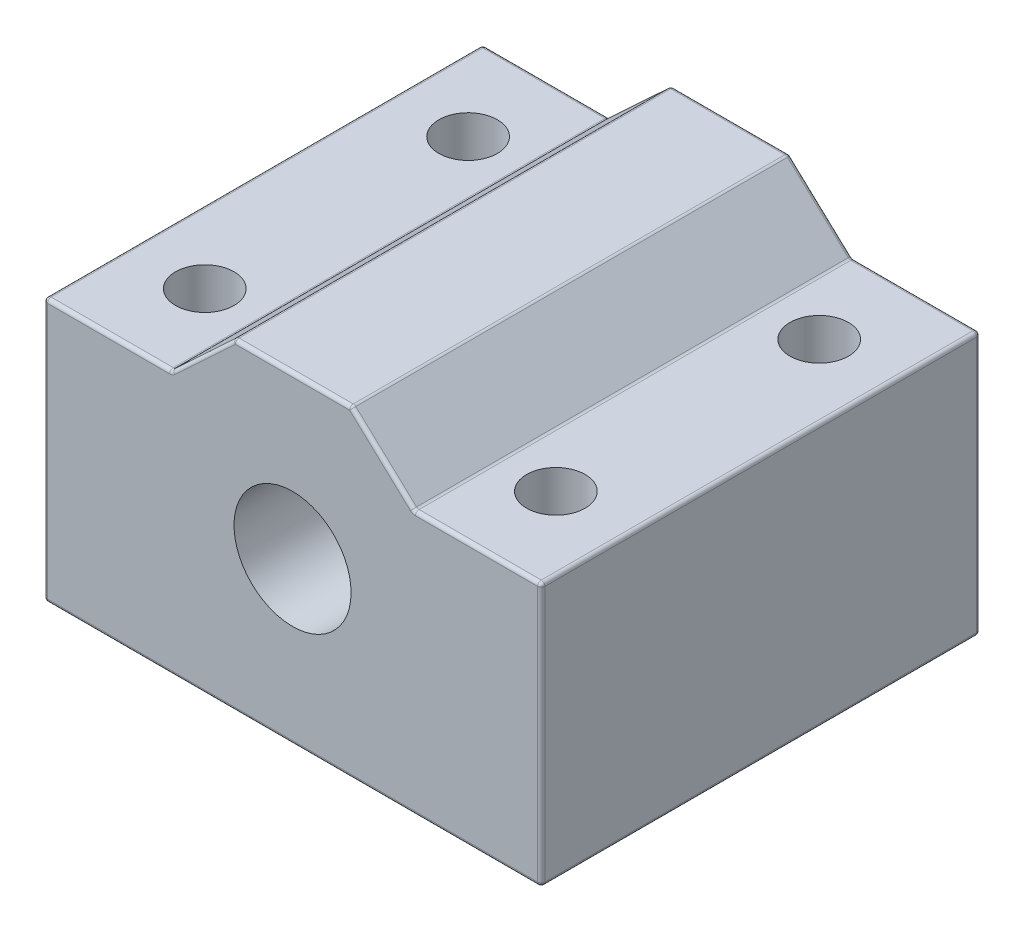
SolidWorks part; units mm, degrees
ref_plane "Front Plane" through (0, 0, 0) normal (0, 0, 1) x (1, 0, 0)
ref_plane "Top Plane" through (0, 0, 0) normal (0, 1, 0) x (1, 0, 0)
ref_plane "Right Plane" through (0, 0, 0) normal (1, 0, 0) x (0, 0, -1)
sketch "Sketch1" plane through (0, 0, 0) normal (0, 0, 1) x (1, 0, 0)
  line L0 (17, -11) -> (-17, -11)
  line L1 (-17, -11) -> (-17, 7)
  line L2 (17, -11) -> (17, 7)
  line L3 (4, 11) -> (-4, 11)
  line L5 (8.3, 7) -> (17, 7)
  line L6 (8.3, 7) -> (4, 11)
  line L7 (-8.3, 7) -> (-17, 7)
  line L8 (-8.3, 7) -> (-4, 11)
  circle A0 centre (0, 0) radius 4
extrude "Boss-Extrude1" add sketch "Sketch1" along normal mid plane 30
sketch "Sketch2" plane through (0, -11, 0) normal (0, -1, 0) x (1, 0, 0)
  circle A0 centre (12, 9) radius 2
  circle A1 centre (-12, 9) radius 2
  circle A2 centre (12, -9) radius 2
  circle A3 centre (-12, -9) radius 2
extrude "Cut-Extrude1" cut sketch "Sketch2" against normal up to next
fillet "Fillet1" radius 0.25 24 edges at (12.65, 7, 15) (-6.15, 9, 15) (17, -11, 0) (0, -11, 15) (-17, -11, 0) (0, -11, -15) (-17, -2, -15) (17, -2, -15) (-17, -2, 15) (17, -2, 15) (-12.65, 7, -15) (-6.15, 9, -15) (0, 11, -15) (6.15, 9, -15) (12.65, 7, -15) (6.15, 9, 15) (0, 11, 15) (-12.65, 7, 15) (-8.3, 7, 0) (-17, 7, 0) (-4, 11, 0) (4, 11, 0) (8.3, 7, 0) (17, 7, 0)
